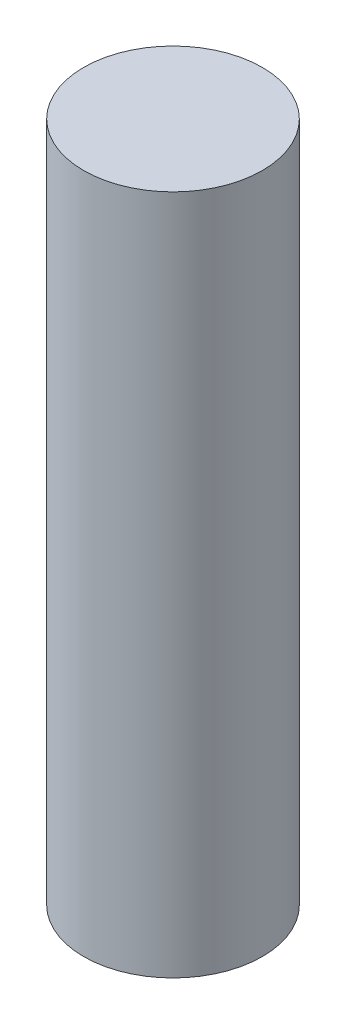
SolidWorks part; units mm, degrees
ref_plane "Front Plane" through (0, 0, 0) normal (0, 0, 1) x (1, 0, 0)
ref_plane "Top Plane" through (0, 0, 0) normal (0, 1, 0) x (1, 0, 0)
ref_plane "Right Plane" through (0, 0, 0) normal (1, 0, 0) x (0, 0, -1)
sketch "Sketch1" plane through (0, 0, 0) normal (0, 1, 0) x (1, 0, 0)
  circle A0 centre (0, 0) radius 1.05
  dimension "D1" = 2.1
extrude "Boss-Extrude1" add sketch "Sketch1" along normal blind 8
